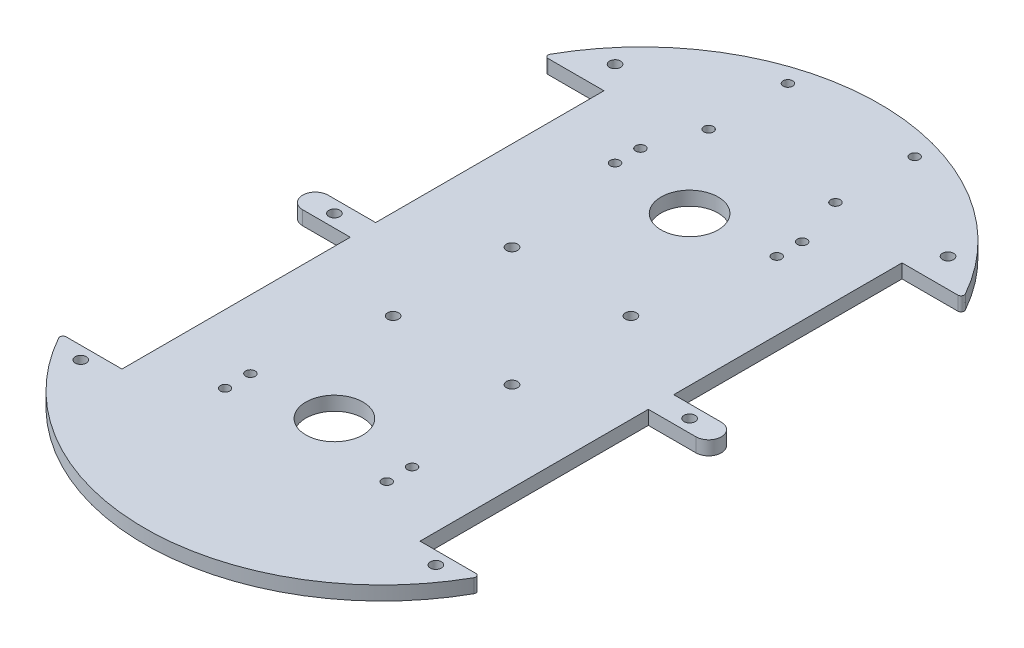
SolidWorks part; units mm, degrees
material "ABS PC"
ref_plane "Front Plane" through (0, 0, 0) normal (0, 0, 1) x (1, 0, 0)
ref_plane "Top Plane" through (0, 0, 0) normal (0, 1, 0) x (1, 0, 0)
ref_plane "Right Plane" through (0, 0, 0) normal (1, 0, 0) x (0, 0, -1)
ref_plane "Plane1" through (0, 4.4, 0) normal (0, 1, 0) x (1, 0, 0)
sketch "Sketch2" plane through (0, 0, 0) normal (0, 1, 0) x (1, 0, 0)
  line L1 (-66, 116) -> (66, 116)
  line L2 (-66, 116) -> (-66, -116)
  line L3 (-66, -116) -> (66, -116)
  line L4 (66, 116) -> (66, -116)
  point P4 (66, 0)
  point P6 (0, 116)
  dimension "D1" = 132
  dimension "D2" = 232
extrude "Plate Size" add sketch "Sketch2" along normal up to surface (4.4 mm away) up to plane "Plane1"
sketch "Sketch4" plane through (0, 0, 0) normal (0, 1, 0) x (1, 0, 0)
  line L0 (-66, 116) -> (-66, -116) construction
  line L1 (66, 116) -> (66, -116) construction
  line L2 (0, -40.9051) -> (0, 40.9051) construction
  line L4 (-64.6, 76) -> (-47, 76)
  line L6 (-62, 4) -> (-47, 4)
  line L7 (-47, 76) -> (-47, 4)
  line L8 (-47, -4) -> (-47, 4) construction
  line L9 (64.6, 76) -> (47, 76)
  line L11 (62, 4) -> (47, 4)
  line L12 (47, 76) -> (47, 4)
  line L13 (64.6, -76) -> (47, -76)
  line L15 (62, -4) -> (47, -4)
  line L16 (47, -76) -> (47, -4)
  line L17 (-47, -76) -> (-64.6, -76)
  line L18 (-47, -76) -> (-47, -4)
  line L19 (-47, -4) -> (-62, -4)
  line L21 (47, -4) -> (47, 4) construction
  line L23 (-47, 40) -> (47, 40) construction
  line L24 (0, -2.475) -> (0, 2.475) construction
  arc A0 (65.473, 77.4878) -> (-65.473, 77.4878) centre (0, 40.9051) ccw
  arc A1 (-65.473, -77.4878) -> (65.473, -77.4878) centre (0, -40.9051) ccw
  arc A2 (-62, 4) -> (-62, -4) centre (-62, 0) ccw
  arc A3 (62, -4) -> (62, 4) centre (62, 0) ccw
  arc A4 (-64.6, -76) -> (-65.473, -77.4878) centre (-64.6, -77) ccw
  arc A5 (65.473, -77.4878) -> (64.6, -76) centre (64.6, -77) ccw
  arc A6 (64.6, 76) -> (65.473, 77.4878) centre (64.6, 77) ccw
  arc A7 (-65.473, 77.4878) -> (-64.6, 76) centre (-64.6, 77) ccw
  point P2 (0, 0)
  point P33 (-47, 0)
  point P39 (0, 40)
  dimension "D1" = 150
  dimension "D2" = 231.8102
  dimension "D6" = 2
  dimension "D3" = 72
  dimension "D4" = 8
  dimension "D5" = 94
extrude "Outer Profile" cut sketch "Sketch4" along normal through all flip side to cut
hole_wizard "M3 Clearance Hole1" positions "Sketch5" profile "Sketch6" hole size "M3" standard "ANSI Metric" end condition through all
sketch "Sketch5" plane through (0, 0, 0) normal (0, 1, 0) x (1, 0, 0)
  line L1 (-56, -80) -> (56, -80) construction
  line L5 (0, -2.42) -> (0, 2.42) construction
  line L7 (-2.42, 0) -> (2.42, 0) construction
  line L8 (-52.5, 85) -> (52.5, 85) construction
  line L10 (56, 0) -> (-56, 0) construction
  circle A0 centre (-56, -80) radius 1.75 construction
  point P0 (-56, -80)
  point P159 (56, -80)
  point P161 (0, -80)
  point P171 (-52.5, 85)
  point P177 (52.5, 85)
  point P179 (0, 85)
  point P184 (-56, 0)
  point P186 (56, 0)
  point P192 (0, 0)
  dimension "D1" = 80
  dimension "D3" = 3.5
  dimension "D2" = 56
  dimension "D4" = 52.5
  dimension "D5" = 85
sketch "Sketch6" plane through (-56, 0, 80) normal (1, 0, 0) x (0, 0, -1)
  line L0 (0, 0) -> (0, 4.4)
  line L1 (0, 4.4) -> (1.75, 4.4)
  line L2 (1.75, 4.4) -> (1.75, 0)
  line L5 (1.75, 0) -> (0, 0)
  line L11 (0, -6.35) -> (0, 107.95) construction
  dimension "Thru Hole Dia." = 3.5
  dimension "Thru Hole Depth" = 4.4
hole_wizard "Ø18.0 (18) Diameter Hole4" positions "Sketch9" profile "Sketch10" hole size "Ø18.0" standard "ANSI Metric" end condition through all
sketch "Sketch9" plane through (0, 0, 0) normal (0, 1, 0) x (1, 0, 0)
  line L0 (0, -2.42) -> (0, 2.42) construction
  line L1 (0, -56) -> (0, 56) construction
  line L3 (-2.42, 0) -> (2.42, 0) construction
  point P0 (0, 56)
  point P2 (0, -56)
  point P10 (0, 0)
  dimension "D1" = 56
sketch "Sketch10" plane through (0, 0, -56) normal (1, 0, 0) x (0, 0, -1)
  line L0 (0, 0) -> (0, 4.4)
  line L1 (0, 4.4) -> (9, 4.4)
  line L2 (9, 4.4) -> (9, 0)
  line L5 (9, 0) -> (0, 0)
  line L11 (0, -6.35) -> (0, 107.95) construction
  dimension "Thru Hole Dia." = 18
  dimension "Thru Hole Depth" = 4.4
hole_wizard "M3 Clearance Hole2" positions "Sketch11" profile "Sketch12" hole size "M3" standard "ANSI Metric" end condition through all
sketch "Sketch11" plane through (0, 0, 0) normal (0, 1, 0) x (1, 0, 0)
  line L1 (18.75, 18.75) -> (-18.75, 18.75) construction
  line L2 (18.75, 18.75) -> (18.75, -18.75) construction
  line L3 (18.75, -18.75) -> (-18.75, -18.75) construction
  line L4 (-18.75, 18.75) -> (-18.75, -18.75) construction
  line L5 (0, -2.42) -> (0, 2.42) construction
  line L6 (-2.42, 0) -> (2.42, 0) construction
  point P0 (18.75, 18.75)
  point P4 (-18.75, -18.75)
  point P31 (18.75, -18.75)
  point P32 (-18.75, 18.75)
  point P39 (0, 18.75)
  point P42 (18.75, 0)
  dimension "D1" = 37.5
sketch "Sketch12" plane through (18.75, 0, -18.75) normal (1, 0, 0) x (0, 0, -1)
  line L0 (0, 0) -> (0, 4.4)
  line L1 (0, 4.4) -> (1.75, 4.4)
  line L2 (1.75, 4.4) -> (1.75, 0)
  line L5 (1.75, 0) -> (0, 0)
  line L11 (0, -6.35) -> (0, 107.95) construction
  dimension "Thru Hole Dia." = 3.5
  dimension "Thru Hole Depth" = 4.4
hole_wizard "M3 Clearance Hole3" positions "Sketch13" profile "Sketch14" hole size "M3" standard "ANSI Metric" end condition through all
sketch "Sketch13" plane through (0, 0, 0) normal (0, 1, 0) x (1, 0, 0)
  line L1 (-25.5, 66) -> (25.5, 66) construction
  line L2 (-25.5, 66) -> (-25.5, -65) construction
  line L3 (-25.5, -65) -> (25.5, -65) construction
  line L4 (25.5, 66) -> (25.5, -65) construction
  line L5 (0, -2.42) -> (0, 2.42) construction
  line L7 (25.5, -57) -> (25.5, -65) construction
  line L10 (-25.5, -65) -> (-25.5, -57) construction
  line L13 (-25.5, 66) -> (-25.5, 58) construction
  line L16 (25.5, 58) -> (25.5, 66) construction
  point P0 (-25.5, 66)
  point P4 (25.5, -65)
  point P125 (-25.5, -65)
  point P126 (25.5, 66)
  point P128 (0, 66)
  point P140 (-25.5, 58)
  point P142 (25.5, 58)
  point P144 (25.5, -57)
  point P146 (-25.5, -57)
  dimension "D1" = 51
  dimension "D2" = 131
  dimension "D3" = 8
  dimension "D4" = 65
sketch "Sketch14" plane through (-25.5, 0, -66) normal (1, 0, 0) x (0, 0, -1)
  line L0 (0, 0) -> (0, 4.4)
  line L1 (0, 4.4) -> (1.5, 4.4)
  line L2 (1.5, 4.4) -> (1.5, 0)
  line L5 (1.5, 0) -> (0, 0)
  line L11 (0, -6.35) -> (0, 107.95) construction
  dimension "Thru Hole Dia." = 3
  dimension "Thru Hole Depth" = 4.4
hole_wizard "M3 Clearance Hole4" positions "Sketch15" profile "Sketch16" hole size "M3" standard "ANSI Metric" end condition through all
sketch "Sketch15" plane through (0, 0, 0) normal (0, 1, 0) x (1, 0, 0)
  line L1 (-20, 107) -> (20, 107) construction
  line L2 (-20, 107) -> (-20, 82) construction
  line L3 (-20, 82) -> (20, 82) construction
  line L4 (20, 107) -> (20, 82) construction
  line L5 (0, -2.42) -> (0, 2.42) construction
  line L6 (-66, 116) -> (66, 116) construction
  point P0 (-20, 107)
  point P65 (0, 82)
  point P74 (20, 107)
  point P77 (-20, 82)
  point P80 (20, 82)
  dimension "D1" = 40
  dimension "D2" = 25
  dimension "D3" = 9
sketch "Sketch16" plane through (-20, 0, -107) normal (1, 0, 0) x (0, 0, -1)
  line L0 (0, 0) -> (0, 4.4)
  line L1 (0, 4.4) -> (1.5, 4.4)
  line L2 (1.5, 4.4) -> (1.5, 0)
  line L5 (1.5, 0) -> (0, 0)
  line L11 (0, -6.35) -> (0, 107.95) construction
  dimension "Thru Hole Dia." = 3
  dimension "Thru Hole Depth" = 4.4
